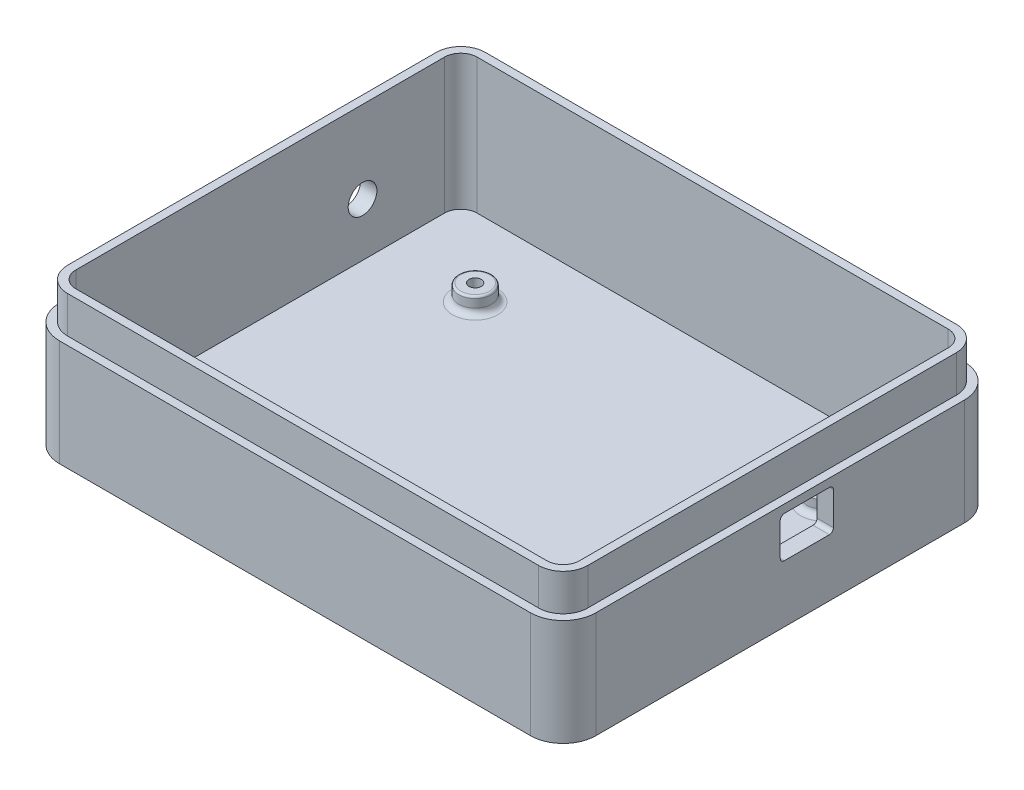
SolidWorks part; units mm, degrees
ref_plane "Alzado" through (0, 0, 0) normal (0, 0, 1) x (1, 0, 0)
ref_plane "Planta" through (0, 0, 0) normal (0, 1, 0) x (1, 0, 0)
ref_plane "Vista lateral" through (0, 0, 0) normal (1, 0, 0) x (0, 0, -1)
sketch "Croquis1" plane through (0, 0, 0) normal (0, 1, 0) x (1, 0, 0)
  line L0 (0, 0) -> (42.5, 0) construction
  line L1 (-42.5, 30) -> (42.5, 30) construction
  line L2 (-42.5, 30) -> (-42.5, -30) construction
  line L3 (-42.5, -30) -> (42.5, -30) construction
  line L4 (42.5, 30) -> (42.5, -30) construction
  line L5 (-42.5, 30) -> (42.5, -30) construction
  line L6 (-42.5, -30) -> (42.5, 30) construction
  line L7 (0, 0) -> (0, 30) construction
  line L8 (52.5, 40) -> (52.5, -40) construction
  line L9 (-52.5, -40) -> (52.5, -40) construction
  line L10 (-52.5, 40) -> (-52.5, -40) construction
  line L11 (-52.5, 40) -> (52.5, 40) construction
  line L12 (65.5, 53) -> (65.5, -53)
  line L13 (-65.5, -53) -> (65.5, -53)
  line L14 (-65.5, 53) -> (-65.5, -53)
  line L15 (-65.5, 53) -> (65.5, 53)
  circle A0 centre (42.5, -30) radius 1.5
  circle A1 centre (42.5, 30) radius 1.5
  circle A2 centre (-42.5, 30) radius 1.5
  circle A3 centre (-42.5, -30) radius 1.5
  point P0 (0, 0)
  dimension "D3" = 3
  dimension "D1" = 60
  dimension "D2" = 85
  dimension "D4" = 10
  dimension "D5" = 13
extrude "Saliente-Extruir1" add sketch "Croquis1" along normal blind 26 contours L15 L14 L13 L12 A1 A0 A2 A3 | A3 | A2 | A1 | A0
fillet "Redondeo2" radius 8 4 edges at (65.5, 13, -53) (65.5, 13, 53) (-65.5, 13, 53) (-65.5, 13, -53)
shell "Vaciado1" thickness 2
sketch "Croquis3" plane through (0, 2, 0) normal (0, 1, 0) x (1, 0, 0)
  line L2 (0, 0) -> (34.456, 0) construction
  line L3 (0, 0) -> (0, 38.5334) construction
  circle A0 centre (46, 30) radius 1.5
  circle A3 centre (46, 30) radius 4
  circle A5 centre (-39, 30) radius 1.5
  circle A8 centre (-39, 30) radius 4
  circle A9 centre (46, -30) radius 1.5
  circle A10 centre (46, -30) radius 4
  circle A11 centre (-39, -30) radius 1.5
  circle A12 centre (-39, -30) radius 4
  point P4 (0, 0)
  dimension "D1" = 2.5
  dimension "D4" = 3
  dimension "D5" = 3
  dimension "D6" = 2.5
  dimension "D2" = 39
  dimension "D3" = 30
  dimension "D7" = 85
extrude "Saliente-Extruir2" add sketch "Croquis3" along normal blind 4
fillet "Redondeo4" radius 1.5 4 edges at (-39, 2, -26) (46, 2, 26) (46, 2, -26) (-39, 2, 26)
fillet "Redondeo5" radius 0.5 4 edges at (-39, 6, -26) (46, 6, -26) (-39, 6, 26) (46, 6, 26)
sketch "Croquis4" plane through (0, 2, 0) normal (0, 1, 0) x (1, 0, 0)
  line L11 (-57.5, -51) -> (57.5, -51) construction
  line L12 (63.5, 45) -> (63.5, -45) construction
  line L13 (-57.5, 51) -> (57.5, 51) construction
  line L14 (-63.5, 45) -> (-63.5, -45) construction
  line L15 (-61.5, 45) -> (-61.5, -45)
  line L16 (-57.5, -49) -> (57.5, -49)
  line L17 (61.5, -45) -> (61.5, 45)
  line L18 (57.5, 49) -> (-57.5, 49)
  line L19 (-61.5, 45) -> (-61.5, -45)
  line L20 (-57.5, -49) -> (57.5, -49)
  line L21 (61.5, -45) -> (61.5, 45)
  line L22 (57.5, 49) -> (-57.5, 49)
  line L23 (-57.5, -51) -> (57.5, -51)
  line L24 (63.5, 45) -> (63.5, -45)
  line L25 (-57.5, 51) -> (57.5, 51)
  line L26 (-63.5, 45) -> (-63.5, -45)
  arc A10 (-63.5, -45) -> (-57.5, -51) centre (-57.5, -45) ccw construction
  arc A11 (63.5, 45) -> (57.5, 51) centre (57.5, 45) ccw construction
  arc A12 (-57.5, 51) -> (-63.5, 45) centre (-57.5, 45) ccw construction
  arc A13 (-63.5, -45) -> (-57.5, -51) centre (-57.5, -45) ccw
  arc A14 (-61.5, -45) -> (-57.5, -49) centre (-57.5, -45) ccw
  arc A15 (57.5, -49) -> (61.5, -45) centre (57.5, -45) ccw
  arc A16 (61.5, 45) -> (57.5, 49) centre (57.5, 45) ccw
  arc A17 (-57.5, 49) -> (-61.5, 45) centre (-57.5, 45) ccw
  arc A18 (-61.5, -45) -> (-57.5, -49) centre (-57.5, -45) ccw
  arc A19 (57.5, -49) -> (61.5, -45) centre (57.5, -45) ccw
  arc A20 (61.5, 45) -> (57.5, 49) centre (57.5, 45) ccw
  arc A21 (-57.5, 49) -> (-61.5, 45) centre (-57.5, 45) ccw
  arc A22 (63.5, 45) -> (57.5, 51) centre (57.5, 45) ccw
  arc A23 (-57.5, 51) -> (-63.5, 45) centre (-57.5, 45) ccw
  line M13 (57.5, 51) -> (-57.5, 51)
  arc M14 (-57.5, 51) -> (-63.5, 45) centre (-57.5, 45) ccw
  line M15 (-63.5, 45) -> (-63.5, -45)
  arc M16 (-63.5, -45) -> (-57.5, -51) centre (-57.5, -45) ccw
  line M17 (-57.5, -51) -> (57.5, -51)
  arc M18 (57.5, -51) -> (63.5, -45) centre (57.5, -45) ccw
  line M19 (63.5, -45) -> (63.5, 45)
  arc M20 (63.5, 45) -> (57.5, 51) centre (57.5, 45) ccw
  dimension "D1" = 2
extrude "Saliente-Extruir3" add sketch "Croquis4" along normal blind 33 contours A21 L22 A20 L21 A19 L20 A18 L19 M20 M13 M14 M15 M16 M17 M18 M19
sketch "Croquis5" plane through (65.5, 0, 0) normal (1, 0, 0) x (0, 0, -1)
  line L0 (-53, 0) -> (-53, 26) construction
  line L1 (-53, 0) -> (-53, 26) construction
  line L2 (45, 0) -> (-45, 0) construction
  line L3 (1, 24) -> (12, 24)
  line L4 (0, 23) -> (0, 15)
  line L5 (1, 14) -> (12, 14)
  line L6 (13, 23) -> (13, 15)
  line L7 (0, 24) -> (13, 14) construction
  line L8 (0, 14) -> (13, 24) construction
  arc A0 (12, 24) -> (13, 23) centre (12, 23) cw
  arc A1 (12, 14) -> (13, 15) centre (12, 15) ccw
  arc A2 (0, 15) -> (1, 14) centre (1, 15) ccw
  arc A3 (1, 24) -> (0, 23) centre (1, 23) ccw
  point P2 (6.5, 19)
  dimension "D5" = 1
  dimension "D1" = 53
  dimension "D2" = 14
  dimension "D3" = 24
  dimension "D4" = 13
extrude "Cortar-Extruir2" cut sketch "Croquis5" against normal up to next
sketch "Croquis7" plane through (-65.5, 0, 0) normal (-1, 0, 0) x (0, 0, 1)
  line L0 (-45, 0) -> (45, 0) construction
  circle A0 centre (-25, 15) radius 3.5
  dimension "D1" = 7
  dimension "D2" = 15
  dimension "D3" = 25
extrude "Cortar-Extruir3" cut sketch "Croquis7" against normal up to next
